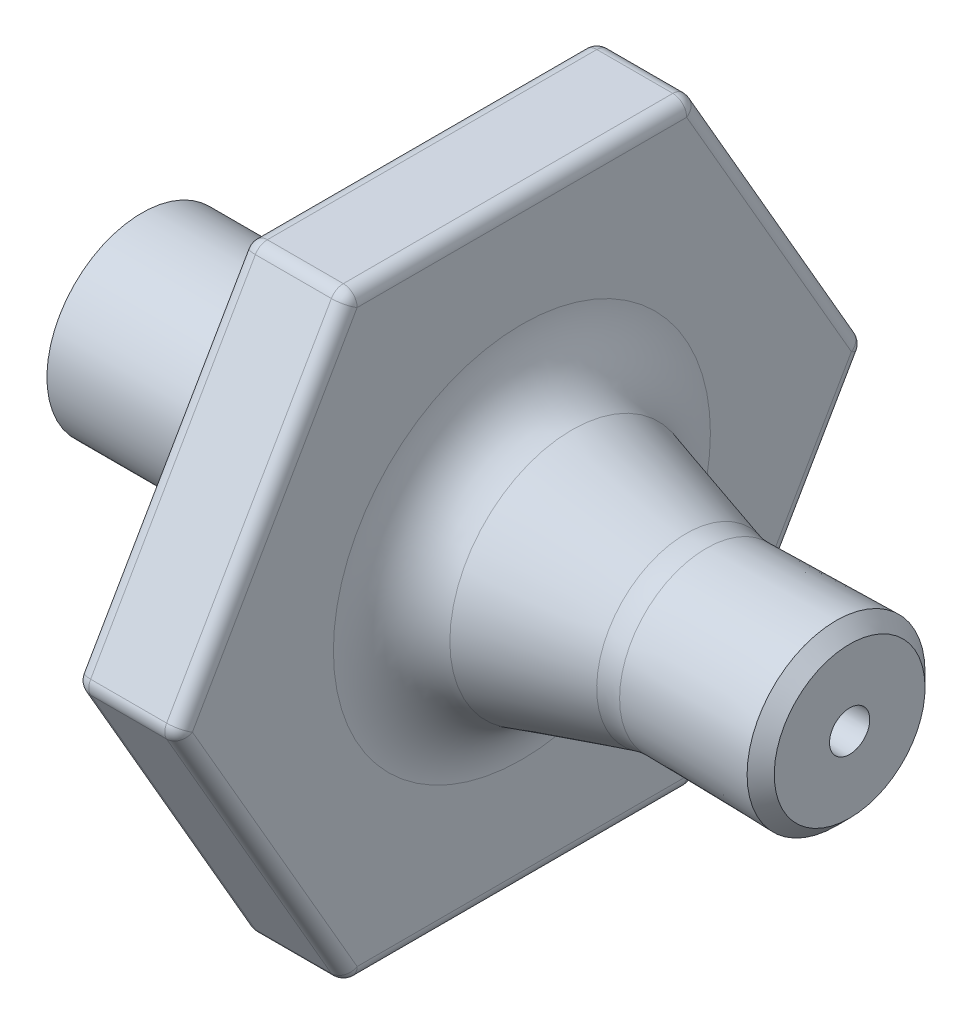
SolidWorks part; units mm, degrees
ref_plane "Front Plane" through (0, 0, 0) normal (0, 0, 1) x (1, 0, 0)
ref_plane "Top Plane" through (0, 0, 0) normal (0, 1, 0) x (1, 0, 0)
ref_plane "Right Plane" through (0, 0, 0) normal (1, 0, 0) x (0, 0, -1)
sketch "Sketch1" plane through (0, 0, 0) normal (0, 0, 1) x (1, 0, 0)
  line L0 (0, 1.95) -> (10.7189, 1.95)
  line L1 (0, -55) -> (0, 55) construction
  line L2 (10.7189, 1.95) -> (15.7757, 0.5)
  line L4 (15.7757, 0.5) -> (20.4878, 0.5823)
  line L8 (55, 0) -> (-55, 0) construction
  line L9 (0, 0) -> (20.4878, 0) construction
  line L10 (20.4878, 0.5823) -> (20.4878, 0) construction
  line L11 (0, 3.95) -> (11, 3.95) construction
  line L12 (11, 3.95) -> (16.0396, 2.5049)
  line L13 (16.0396, 2.5049) -> (20.4878, 2.5826)
  line L14 (0, 0) -> (0, 1.95) construction
  line L15 (20.4878, 0.5823) -> (11.9148, 0.5823) construction
  line L16 (0, 1.95) -> (0, 2.75)
  line L17 (11, 3.95) -> (11, 10)
  line L18 (11, 10) -> (8, 10)
  line L19 (8, 10) -> (8, 2.75)
  line L20 (0, 2.75) -> (8, 2.75)
  line L21 (0, 2.75) -> (0, 3.95) construction
  line L22 (16.0396, 2.5049) -> (20.4529, 2.5819) construction
  line L23 (20.4878, 0.5823) -> (20.4878, 2.5826)
  dimension "D1" = 0.5
  dimension "D2" = 0.5823
  dimension "D3" = 2
  dimension "D4" = 2.75
  dimension "D5" = 0.8
  dimension "D6" = 3
  dimension "D7" = 16
  dimension "D8" = 1
  dimension "D9" = 10
  dimension "D10" = 8
revolve "Revolve1" add sketch "Sketch1" angle 360 about L9
fillet "Fillet4" radius 3 2 edges at (15.7757, -0.5, 0) (10.7189, -1.95, 0)
chamfer "Chamfer1" distance 0.4 angle 45 1 edges at (20.4878, -2.5826, 0)
sketch "Sketch2" plane through (11, 0, 0) normal (1, 0, 0) x (0, 0, -1)
  line L0 (0, 0) -> (10, 0) construction
  line L1 (10, 0) -> (5, 8.6603)
  line L2 (5, 8.6603) -> (-5, 8.6603)
  line L3 (-5, 8.6603) -> (-10, 0)
  line L4 (-10, 0) -> (-5, -8.6603)
  line L5 (-5, -8.6603) -> (5, -8.6603)
  line L6 (5, -8.6603) -> (10, 0)
  circle A0 centre (0, 0) radius 8.6603 construction
  circle A1 centre (0, 0) radius 10 construction
  circle A2 centre (0, 0) radius 10
  circle M2 centre (0, 0) radius 10
extrude "Cut-Extrude1" cut sketch "Sketch2" against normal through all both and the other way through all contours L3 M2 | L2 M2 | L1 M2 | L4 M2 | L5 M2 | L6 M2
fillet "Fillet5" radius 0.4 18 edges at (9.5, 8.6603, -5) (9.5, 0, -10) (9.5, -8.6603, -5) (9.5, -8.6603, 5) (9.5, 0, 10) (9.5, 8.6603, 5) (8, -8.6603, 0) (8, -4.3301, 7.5) (8, 4.3301, -7.5) (8, -4.3301, -7.5) (8, 8.6603, 0) (8, 4.3301, 7.5) (11, 8.6603, 0) (11, 4.3301, -7.5) (11, -4.3301, -7.5) (11, -8.6603, 0) (11, -4.3301, 7.5) (11, 4.3301, 7.5)
fillet "Fillet6" radius 2 2 edges at (16.0396, -2.5049, 0) (11, -3.95, 0)
